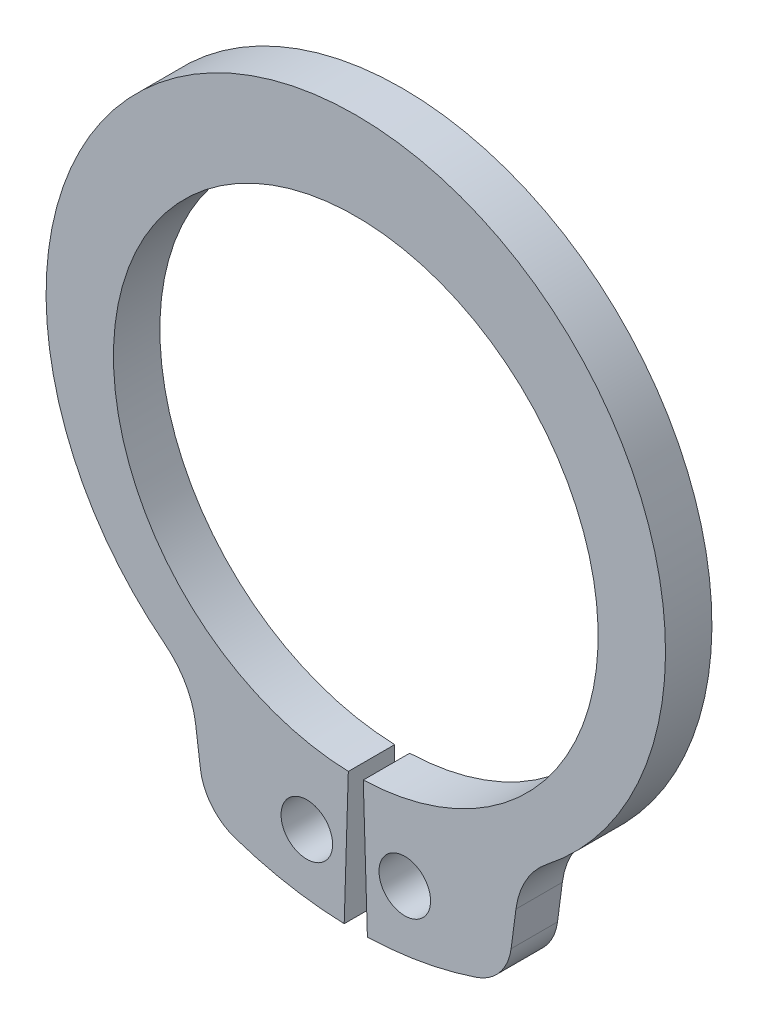
SolidWorks part; units mm, degrees
ref_plane "Plane1" through (0, 0, 0) normal (0, 0, 1) x (1, 0, 0)
ref_plane "Plane2" through (0, 0, 0) normal (0, 1, 0) x (1, 0, 0)
ref_plane "Plane3" through (0, 0, 0) normal (1, 0, 0) x (0, 0, -1)
sketch "Clipboard" plane through (0, 0, 0) normal (0, 0, 1) x (1, 0, 0)
  line L0 (0, 0) -> (1.7, 0)
  line L1 (0, 0) -> (0, 1)
  line L2 (0, 0) -> (0, -2.6)
  circle A0 centre (0, 0) radius 0.5
  circle A1 centre (0, 0) radius 5
  dimension "HoleDia" = 1
  dimension "ShaftDia" = 10
  dimension "LargeSection" = 1.7
  dimension "SmallSection" = 1
  dimension "LugSection" = 2.6
sketch "BodySke" plane through (0, 0, 0) normal (0, 0, 1) x (1, 0, 0)
  line L0 (-1.5431, 0) -> (1.5431, 0) construction
  line L1 (0, 0) -> (0, 6.4) construction
  line L2 (0.1449, -4.6978) -> (0.225, -7.2965)
  line L3 (-0.1449, -4.6978) -> (-0.225, -7.2965)
  line L4 (0, 0) -> (4.6911, -5.5931) construction
  line L5 (0, 0) -> (-4.6911, -5.5931) construction
  line L7 (3.1059, -5.3844) -> (3.012, -6.0977)
  line L8 (-3.1059, -5.3844) -> (-3.012, -6.0977)
  circle A0 centre (0, 0) radius 4.7 construction
  arc A1 (0.1449, -4.6978) -> (-0.1449, -4.6978) centre (0, 0) ccw
  arc A2 (3.6629, -4.3672) -> (-3.6629, -4.3672) centre (0, 0.3933) ccw construction
  arc A3 (0.225, -7.2965) -> (2.3413, -6.9143) centre (0, 0) ccw
  arc A4 (3.7049, -4.3346) -> (3.1059, -5.3844) centre (4.6911, -5.5931) ccw
  arc A5 (-3.1059, -5.3844) -> (-3.7049, -4.3346) centre (-4.6911, -5.5931) ccw
  arc A6 (-2.3413, -6.9143) -> (-0.225, -7.2965) centre (0, 0) ccw
  arc A7 (3.7049, -4.3346) -> (-3.7049, -4.3346) centre (0, 0.3933) ccw
  arc A8 (-3.1168, -5.3017) -> (3.1168, -5.3017) centre (0, 0) ccw construction
  circle A9 centre (0.95, -6.0762) radius 0.5
  circle A10 centre (-0.95, -6.0762) radius 0.5
  arc A11 (3.012, -6.0977) -> (2.3413, -6.9143) centre (2.0206, -5.9672) cw
  arc A12 (-3.012, -6.0977) -> (-2.3413, -6.9143) centre (-2.0206, -5.9672) ccw
  point P28 (2.9348, -6.6841)
  point P31 (-2.9348, -6.6841)
  dimension "GrooveDia" = 9.4
  dimension "LugRad" = 7.3
  dimension "HoleOffsetRad" = 6.15
  dimension "HoleDia" = 1
  dimension "D3" = 1
  dimension "LargeRad" = 6.4
  dimension "SmallRad" = 5.7
  dimension "SmallAngle" = 79.975
  dimension "D2" = 15
  dimension "HoleSpacing" = 1.9
  dimension "Gap" = 0.45
extrude "Body" add sketch "BodySke" against normal blind 0.9
sketch "NotSke" plane through (0, 0, 0) normal (0, 0, 1) x (1, 0, 0)
  line L0 (0.95, -5.5762) -> (0.95, -6.5762)
  line L1 (0.95, -6.5762) -> (-0.95, -6.5762)
  line L2 (-0.95, -6.5762) -> (-0.95, -5.5762)
  line L3 (-0.95, -5.5762) -> (0.95, -5.5762)
  circle A0 centre (0.95, -6.0762) radius 0.5 construction
  circle A1 centre (-0.95, -6.0762) radius 0.5 construction
extrude "Notch" [suppressed] cut sketch "NotSke" against normal through all
equation "' \"ShaftDia@Clipboard\" = 10"
equation "' \"Thickness@Body\" = 0.9"
equation "' \"GrooveDia@BodySke\" = 9.4"
equation "' \"LugSection@Clipboard\" = 2.6"
equation "' \"LargeSection@Clipboard\" = 1.7"
equation "' \"SmallSection@Clipboard\" = 1.0"
equation "' \"HoleDia@Clipboard\" = 1.0"
equation "' \"ShaftDia@Clipboard\" = 30"
equation "' \"Thickness@Body\" = 2.4"
equation "' \"GrooveDia@BodySke\" = 28.2"
equation "' \"LugSection@Clipboard\" = 5.6"
equation "' \"LargeSection@Clipboard\" = 4.5"
equation "' \"SmallSection@Clipboard\" = 2.5"
equation "' \"HoleDia@Clipboard\" = 2.3"
equation "\"Gap@BodySke\" =  \"Thickness@Body\" / 2"
equation "\"LargeRad@BodySke\" =  \"GrooveDia@BodySke\" / 2 +  \"LargeSection@Clipboard\""
equation "\"SmallRad@BodySke\" =  \"GrooveDia@BodySke\" / 2 +  \"SmallSection@Clipboard\""
equation "\"LugRad@BodySke\" = \"GrooveDia@BodySke\" / 2 + \"LugSection@Clipboard\""
equation "\"HoleOffsetRad@BodySke\" = (  \"ShaftDia@Clipboard\" / 2 + \"LugRad@BodySke\" ) / 2"
equation "\"HoleSpacing@BodySke\" = \"Gap@BodySke\"  * 2 +  \"HoleDia@Clipboard\""
equation "\"HoleDia@BodySke\" =  \"HoleDia@Clipboard\""
equation "\"SmallAngle@BodySke\" = atn(\"HoleSpacing@BodySke\" / 2 / sqr(\"HoleOffsetRad@BodySke\"  * \"HoleOffsetRad@BodySke\" - (\"HoleSpacing@BodySke\" / 2) * (\"HoleSpacing@BodySke\" / 2) ))  * 9 * ( 180 / 3.141593)"
